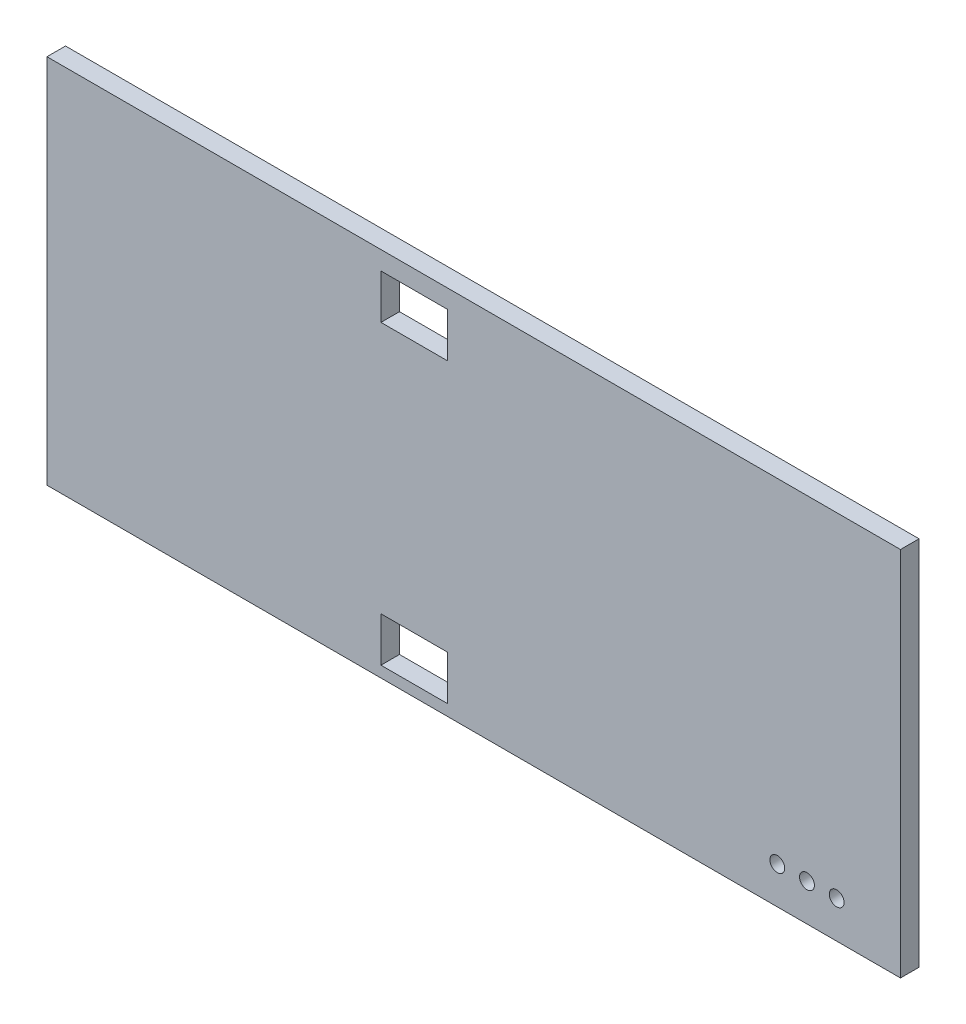
SolidWorks part; units mm, degrees
ref_plane "Front Plane" through (0, 0, 0) normal (0, 0, 1) x (1, 0, 0)
ref_plane "Top Plane" through (0, 0, 0) normal (0, 1, 0) x (1, 0, 0)
ref_plane "Right Plane" through (0, 0, 0) normal (1, 0, 0) x (0, 0, -1)
sketch "Sketch1" plane through (0, 0, 0) normal (0, 0, 1) x (1, 0, 0)
  line L1 (0, 0) -> (292.1, 0)
  line L2 (0, 0) -> (0, 127)
  line L3 (0, 127) -> (292.1, 127)
  line L4 (292.1, 0) -> (292.1, 127)
  dimension "D1" = 292.1
  dimension "D2" = 127
extrude "Boss-Extrude1" add sketch "Sketch1" along normal blind 6.35 contours L3 L4 L1 L2
sketch "Sketch2" plane through (0, 0, 6.35) normal (0, 0, 1) x (1, 0, 0)
  line L1 (114.3, 19.05) -> (137.16, 19.05)
  line L2 (114.3, 19.05) -> (114.3, 3.81)
  line L3 (114.3, 3.81) -> (137.16, 3.81)
  line L4 (137.16, 19.05) -> (137.16, 3.81)
  line L7 (0, 0) -> (0, 127) construction
  line L8 (0, 0) -> (292.1, 0) construction
  dimension "D1" = 3.81
  dimension "D2" = 114.3
  dimension "D3" = 15.24
  dimension "D4" = 22.86
extrude "Cut-Extrude1" cut sketch "Sketch2" against normal blind 6.35
pattern_linear "LPattern1" count 2 spacing 101.6 along (0, 1, 0) of "Cut-Extrude1"
sketch "Sketch3" plane through (0, 0, 6.35) normal (0, 0, 1) x (1, 0, 0)
  line L0 (0, 12.7) -> (292.1, 12.7) construction
  line L1 (0, 0) -> (0, 127) construction
  line L2 (292.1, 0) -> (292.1, 127) construction
  circle A0 centre (249.9406, 12.7) radius 2.54
  circle A1 centre (260.1006, 12.7) radius 2.54
  circle A2 centre (270.2606, 12.7) radius 2.54
  point P12 (270.2606, 12.7)
  dimension "D1" = 5.08
  dimension "D2" = 5.08
  dimension "D3" = 5.08
  dimension "D4" = 10.16
  dimension "D5" = 10.16
  dimension "D6" = 114.3
extrude "Cut-Extrude2" cut sketch "Sketch3" against normal through all
